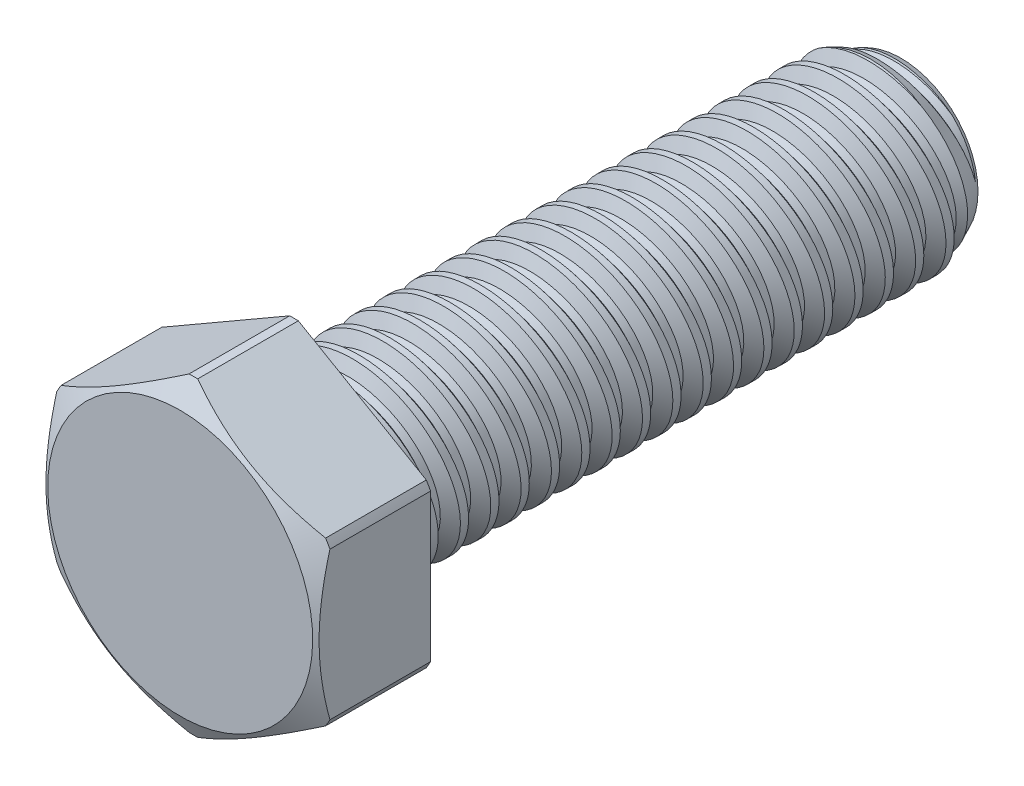
SolidWorks part; units mm, degrees
ref_plane "Front" through (0, 0, 0) normal (0, 0, 1) x (1, 0, 0)
ref_plane "Top" through (0, 0, 0) normal (0, 1, 0) x (1, 0, 0)
ref_plane "Right" through (0, 0, 0) normal (1, 0, 0) x (0, 0, -1)
sketch "Sketch1" plane through (0, 0, 0) normal (1, 0, 0) x (0, 0, -1)
  line L0 (-15.875, 0) -> (-21.8281, 0) construction
  line L1 (-15.875, 0) -> (-15.875, 7.1438) construction
  line L2 (-15.875, 0) -> (-21.8281, 0) construction
  line L3 (-15.875, -4.7625) -> (15.875, -4.7625) construction
  line L4 (-15.875, 0) -> (15.875, 0)
  line L5 (-15.875, 0) -> (-15.875, 4.7625)
  line L6 (-15.875, 4.7625) -> (15.875, 4.7625)
  line L7 (15.875, 0) -> (15.875, 4.7625)
  dimension "Screw Dia" = 9.525
  dimension "Screw Length" = 31.75
  dimension "Head Height" = 5.9531
  dimension "Head Width" = 14.2875
revolve "Revolve1" add sketch "Sketch1" angle 360 about L0
sketch "Sketch2" plane through (0, 0, 0) normal (1, 0, 0) x (0, 0, -1)
  line L0 (-15.875, 4.7625) -> (-15.875, -4.7625) construction
  line L1 (-15.875, -4.7625) -> (-14.2875, -4.7625) construction
  line L2 (-14.2875, -4.7625) -> (-15.875, 4.7625) construction
  line L3 (-15.875, 4.7625) -> (-15.6793, 4.7951) construction
  line L4 (-14.3091, 5.0235) -> (-15.6793, 4.7951)
  line L5 (-15.6793, 4.7951) -> (-15.0487, 4.0291)
  line L6 (-15.0487, 4.0291) -> (-14.6572, 4.0944)
  line L7 (-14.6572, 4.0944) -> (-14.3091, 5.0235)
  line L8 (-14.8529, 4.0617) -> (-14.9942, 4.9093) construction
  line L9 (-15.875, 0) -> (-15.875, 4.7625) construction
  line L10 (-15.875, 4.7625) -> (-14.9697, 4.7625) construction
  line L11 (-14.9697, 4.7625) -> (-13.3822, -4.7625) construction
  line L12 (-13.3822, -4.7625) -> (-14.2875, -4.7625) construction
  line L13 (-15.875, -4.7625) -> (15.875, -4.7625) construction
  line L14 (-15.875, -0.2832) -> (-12.4769, 0.2832) construction
  line L15 (-15.875, 4.7625) -> (15.875, 4.7625) construction
  point P17 (-14.176, 0)
  dimension "D1" = 1.5875
  dimension "Thread Pitch" = 1.5875
  dimension "D3" = 0.3969
  dimension "D4" = 0.1984
  dimension "D5" = 60
revolve "Cut-Revolve1" cut sketch "Sketch2" angle 360 about L14
sketch "Sketch3" plane through (0, 0, 0) normal (1, 0, 0) x (0, 0, -1)
  line L0 (14.3022, 4.7625) -> (15.875, 4.0291)
  line L1 (15.875, 4.0291) -> (15.875, 4.7625)
  line L2 (15.875, 4.7625) -> (14.3022, 4.7625)
  line L3 (-15.875, 4.7625) -> (15.875, 4.7625) construction
  line L4 (15.875, 0) -> (15.875, 4.7625) construction
  line L5 (-15.0487, 4.0291) -> (15.875, 4.0291) construction
  line L6 (14.3022, 4.7625) -> (14.3022, -4.7625) construction
  line L7 (-15.875, -4.7625) -> (15.875, -4.7625) construction
  line L8 (0, 0) -> (14.3022, 0) construction
  dimension "D1" = 25
  dimension "D2" = 9.525
revolve "Cut-Revolve2" cut sketch "Sketch3" angle 360 about L8
pattern_linear "LPattern1" count 2 spacing 1.5875 along (0, 0, 1) count 20 spacing 1.5875 along (0, 0, 1)
sketch "Sketch5" plane through (0, 0, 15.875) normal (0, 0, 1) x (1, 0, 0)
  line L1 (0, 8.2489) -> (-7.1438, 4.1244)
  line L2 (-7.1438, 4.1244) -> (-7.1438, -4.1244)
  line L3 (-7.1438, -4.1244) -> (0, -8.2489)
  line L4 (0, -8.2489) -> (7.1438, -4.1244)
  line L5 (7.1438, -4.1244) -> (7.1438, 4.1244)
  line L6 (7.1438, 4.1244) -> (0, 8.2489)
  circle A0 centre (0, 0) radius 7.1438 construction
  dimension "D1" = 14.2875
extrude "Extrude1" add sketch "Sketch5" along normal up to vertex
sketch "Sketch6" plane through (0, 0, 0) normal (1, 0, 0) x (0, 0, -1)
  line L0 (-21.8281, 6.9294) -> (-21.1397, 8.1219)
  line L1 (-21.1397, 8.1219) -> (-15.875, 8.1219)
  line L2 (-15.875, 8.1219) -> (-15.875, 8.6299)
  line L3 (-15.875, 8.6299) -> (-21.8281, 8.6299)
  line L4 (-21.8281, 8.6299) -> (-21.8281, 6.9294)
  line L5 (-21.8281, 4.1244) -> (-21.8281, 8.2489) construction
  line L6 (-21.8281, 8.2489) -> (-15.875, 8.2489) construction
  line L7 (-15.875, 4.1244) -> (-15.875, 8.2489) construction
  line L8 (0, 0) -> (-21.1397, 0) construction
  line L9 (-15.875, 0) -> (-21.8281, 0) construction
  line L10 (-21.1397, 0) -> (-21.1397, 8.1219) construction
  line L11 (-18.8516, 8.6299) -> (-18.8516, 0) construction
  dimension "D1" = 30
  dimension "D2" = 0.127
  dimension "D3" = 0.508
  dimension "D4" = 13.8589
  dimension "D5" = 5.9531
  dimension "D6" = 31.75
revolve "Cut-Revolve3" cut sketch "Sketch6" angle 360 about L8
equation "\"D3@Sketch2\"=\"Thread Pitch@Sketch2\"/4"
equation "\"D4@Sketch2\"=\"Thread Pitch@Sketch2\"/8"
equation "\"D1@Sketch2\"=\"Thread Pitch@Sketch2\""
equation "\"D3@LPattern1\"=\"Thread Pitch@Sketch2\""
equation "\"D4@LPattern1\"=\"Thread Pitch@Sketch2\""
equation "\"D4@Sketch6\"=\"Head Width@Sketch1\"*.97"
equation "\"D2@LPattern1\"=\"Screw Length@Sketch1\"/\"Thread Pitch@Sketch2\""
